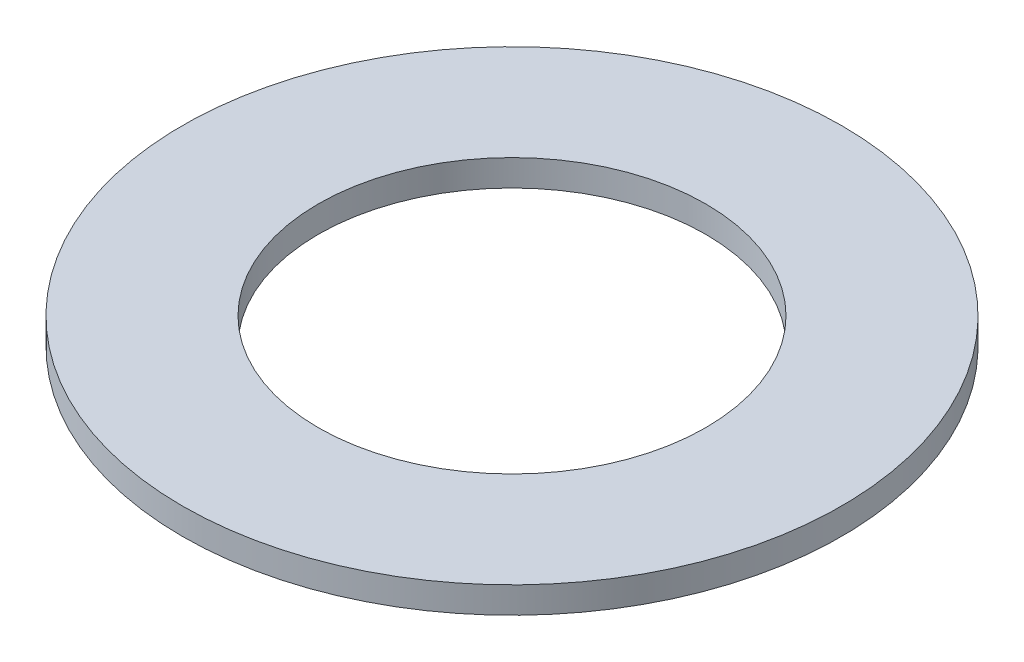
SolidWorks part; units mm, degrees
ref_plane "Front" through (0, 0, 0) normal (0, 0, 1) x (1, 0, 0)
ref_plane "Top" through (0, 0, 0) normal (0, 1, 0) x (1, 0, 0)
ref_plane "Right" through (0, 0, 0) normal (1, 0, 0) x (0, 0, -1)
sketch "Sketch1" plane through (0, 0, 0) normal (0, 1, 0) x (1, 0, 0)
  circle A0 centre (0, 0) radius 12.5
  circle A1 centre (0, 0) radius 7.35
  dimension "D1" = 25
  dimension "D2" = 14.7
extrude "Boss-Extrude1" add sketch "Sketch1" along normal blind 1
